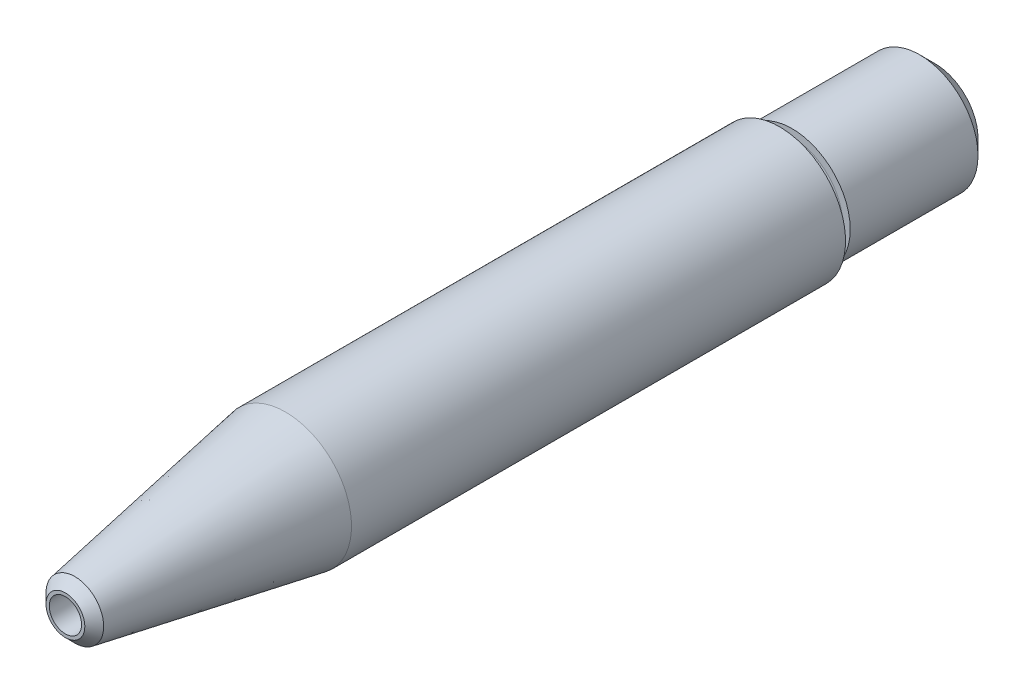
SolidWorks part; units mm, degrees
material "6061-T6 (SS)"
ref_plane "Front Plane" through (0, 0, 0) normal (0, 0, 1) x (1, 0, 0)
ref_plane "Top Plane" through (0, 0, 0) normal (0, 1, 0) x (1, 0, 0)
ref_plane "Right Plane" through (0, 0, 0) normal (1, 0, 0) x (0, 0, -1)
sketch "Sketch19" plane through (0, 0, 0) normal (0, 1, 0) x (1, 0, 0)
  line L0 (0, -0.4662) -> (0, 20.0331) construction
sketch "Sketch1" plane through (0, 0, 0) normal (0, 0, 1) x (1, 0, 0)
  circle A0 centre (0, 0) radius 5.3975
  dimension "D1" = 10.795
extrude "Boss-Extrude1" add sketch "Sketch1" along normal blind 71.12
sketch "Sketch7" plane through (0, 0, 0) normal (0, 1, 0) x (1, 0, 0)
  line L0 (5.3975, -71.12) -> (5.3975, -53.1137)
  line L1 (5.3975, -71.12) -> (2.2225, -71.12)
  line L2 (-5.3975, -71.12) -> (5.3975, -71.12) construction
  line L8 (5.3975, -71.12) -> (5.3975, 0) construction
  line L9 (2.2225, -71.12) -> (5.3975, -53.1137)
  line L10 (0, 47.574) -> (0, -47.574) construction
  dimension "D1" = 10
  dimension "D2" = 3.175
revolve "Cut-Revolve1" cut sketch "Sketch7" angle 360 about L10
sketch "Sketch8" plane through (0, 0, 71.12) normal (0, 0, 1) x (1, 0, 0)
  circle A0 centre (0, 0) radius 1.3208
  dimension "D1" = 2.6416
extrude "Cut-Extrude1" cut sketch "Sketch8" against normal through all
sketch "Sketch10" plane through (0, 0, 0) normal (0, 0, -1) x (-1, 0, 0)
  circle A0 centre (0, 0) radius 4.7625
  circle A1 centre (0, 0) radius 5.3975 construction
  circle A2 centre (0, 0) radius 5.3975
  dimension "D1" = 9.525
extrude "Cut-Extrude2" cut sketch "Sketch10" against normal blind 12.7
hole_wizard "1/4 (0.25) Diameter Hole1" positions "3DSketch2" profile "Sketch17" hole size "1/4" standard "ANSI Inch"
sketch3d "3DSketch2"
  point P0 (0, 0, 0)
sketch "Sketch17" plane through (0, 0, 0) normal (1, 0, 0) x (0, 1, 0)
  line L0 (0, 0) -> (0, 62.8677)
  line L1 (0, 62.8677) -> (3.175, 60.96)
  line L2 (3.175, 60.96) -> (3.175, 0)
  line L5 (3.175, 0) -> (0, 0)
  line L10 (0, 62.8677) -> (-3.175, 60.96) construction
  line L11 (0, -6.35) -> (0, 107.95) construction
  dimension "Hole Dia." = 6.35
  dimension "Hole Depth" = 60.96
  dimension "Drill Angle" = 118
sketch "Sketch18" plane through (0, 0, 0) normal (0, 1, 0) x (1, 0, 0)
  line L0 (4.7625, -12.7) -> (4.7625, 0) construction
  line L1 (5.3975, -12.7) -> (-5.3975, -12.7) construction
  line L2 (4.7625, -12.7) -> (4.7625, 0) construction
  line L3 (5.3975, -12.7) -> (-5.3975, -12.7) construction
  line L4 (4.7625, -12.7) -> (4.1656, -12.7)
  line L5 (4.7625, -11.684) -> (4.1656, -11.684)
  line L6 (4.7625, -12.7) -> (4.7625, -11.684)
  arc A0 (4.1656, -12.7) -> (4.1656, -11.684) centre (4.1656, -12.192) cw
  point P9 (3.6576, -12.192)
  dimension "D2" = 1.1049
  dimension "D3" = 1.016
revolve "Cut-Revolve2" cut sketch "Sketch18" angle 360 about L0
sketch "Sketch20" plane through (0, 0, 0) normal (0, 1, 0) x (1, 0, 0)
  line L0 (4.7625, -11.684) -> (4.7625, 0) construction
  line L1 (4.7625, 0) -> (-4.7625, 0) construction
  line L2 (4.7625, -11.684) -> (4.7625, 0) construction
  line L3 (4.7625, 0) -> (-4.7625, 0) construction
  line L4 (4.7625, 0) -> (4.7625, -1.2319)
  line L5 (4.7625, -1.2319) -> (3.5306, 0)
  line L6 (3.5306, 0) -> (4.7625, 0)
  dimension "D1" = 1.2319
revolve "Cut-Revolve3" cut sketch "Sketch20" angle 360 about L0
chamfer "Chamfer1" distance 0.635 angle 45 1 edges at (-2.2225, 0, 71.12)
